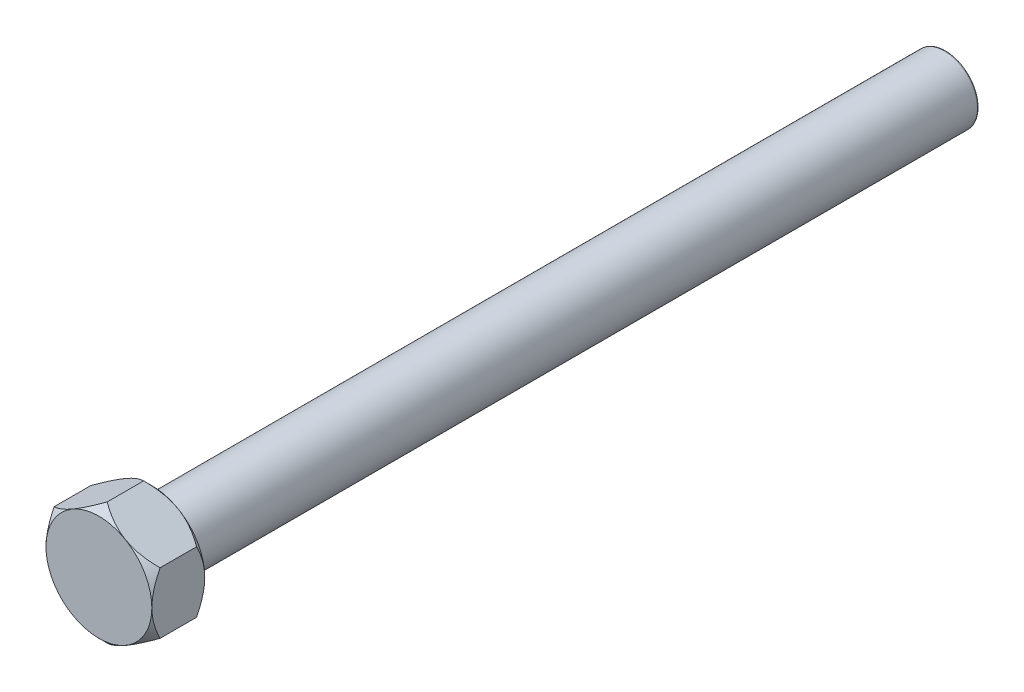
SolidWorks part; units mm, degrees
ref_plane "前视基准面" through (0, 0, 0) normal (0, 0, 1) x (1, 0, 0)
ref_plane "上视基准面" through (0, 0, 0) normal (0, 1, 0) x (1, 0, 0)
ref_plane "右视基准面" through (0, 0, 0) normal (1, 0, 0) x (0, 0, -1)
sketch "草图1" plane through (0, 0, 0) normal (0, 0, 1) x (1, 0, 0)
  line L1 (0, 4.6188) -> (-4, 2.3094)
  line L2 (-4, 2.3094) -> (-4, -2.3094)
  line L3 (-4, -2.3094) -> (0, -4.6188)
  line L4 (0, -4.6188) -> (4, -2.3094)
  line L5 (4, -2.3094) -> (4, 2.3094)
  line L6 (4, 2.3094) -> (0, 4.6188)
  circle A0 centre (0, 0) radius 4 construction
  dimension "D1" = 8
extrude "凸台-拉伸1" add sketch "草图1" along normal blind 4
sketch "草图2" plane through (0, 0, 0) normal (1, 0, 0) x (0, 0, -1)
  line L0 (0, 4.6188) -> (0, 3.9988)
  line L1 (0, 2.3094) -> (0, 4.6188) construction
  line L2 (0, 3.9988) -> (-0.62, 4.6188)
  line L3 (-4, 4.6188) -> (0, 4.6188) construction
  line L4 (-0.62, 4.6188) -> (0, 4.6188)
  line L5 (-3.38, 4.6188) -> (-4, 3.9988)
  line L6 (-4, 2.3094) -> (-4, 4.6188) construction
  line L7 (-4, 3.9988) -> (-4, 4.6188)
  line L8 (-4, 4.6188) -> (-3.38, 4.6188)
  line L9 (0, 0) -> (1.2696, 0) construction
revolve "切除-旋转1" cut sketch "草图2" angle 360 about L9
sketch "草图3" plane through (0, 0, 0) normal (0, 0, -1) x (-1, 0, 0)
  circle A0 centre (0, 0) radius 2.5
extrude "凸台-拉伸2" add sketch "草图3" along normal blind 60
fillet "圆角2" radius 0.12 1 edges at (-2.5, 0, -60)
